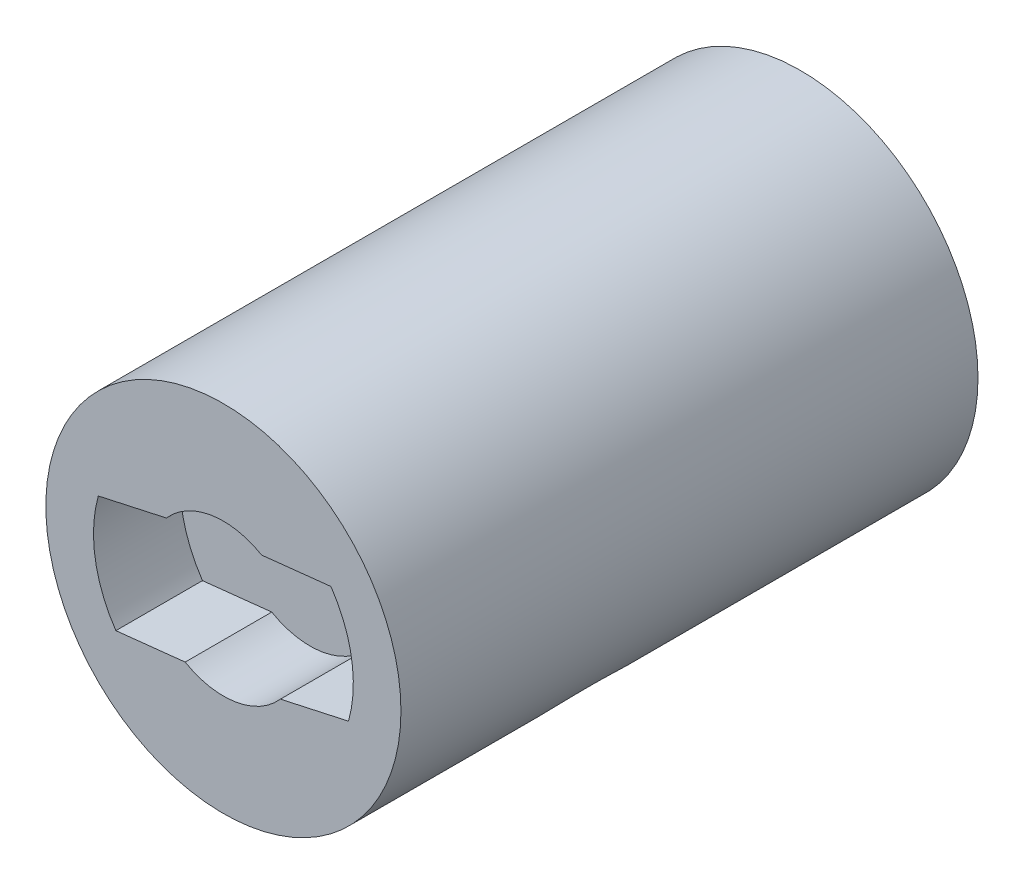
SolidWorks part; units mm, degrees
ref_plane "Спереди" through (0, 0, 0) normal (0, 0, 1) x (1, 0, 0)
ref_plane "Сверху" through (0, 0, 0) normal (0, 1, 0) x (1, 0, 0)
ref_plane "Справа" through (0, 0, 0) normal (1, 0, 0) x (0, 0, -1)
sketch "Эскиз1" plane through (0, 0, 0) normal (0, 0, 1) x (1, 0, 0)
  circle A0 centre (0, 0) radius 8.2
  dimension "D1" = 16.4
extrude "Бобышка-Вытянуть1" add sketch "Эскиз1" along normal blind 26.65
sketch "Эскиз3" plane through (0, 0, 0) normal (0, 0, -1) x (-1, 0, 0)
  circle A0 centre (0, 0) radius 5
  dimension "D1" = 10
extrude "Бобышка-Вытянуть2" add sketch "Эскиз3" along normal blind 1.5
sketch "Эскиз4" plane through (0, 0, 26.65) normal (0, 0, 1) x (1, 0, 0)
  line L8 (-2.6335, 2.3053) -> (-14.3067, -0.2584)
  line L9 (13.648, 4.299) -> (1.765, 3.0224)
  line L10 (2.6335, -2.3053) -> (14.3067, 0.2584)
  line L11 (-13.648, -4.299) -> (-1.765, -3.0224)
  line L12 (-2.6335, 2.3053) -> (-14.3067, -0.2584)
  line L13 (13.648, 4.299) -> (1.765, 3.0224)
  line L14 (2.6335, -2.3053) -> (14.3067, 0.2584)
  line L15 (-13.648, -4.299) -> (-1.765, -3.0224)
  circle A4 centre (0, 0) radius 6
  arc A8 (1.765, 3.0224) -> (-2.6335, 2.3053) centre (0, 0) ccw
  arc A9 (14.3067, 0.2584) -> (13.648, 4.299) centre (13.8669, 2.2607) ccw
  arc A10 (-1.765, -3.0224) -> (2.6335, -2.3053) centre (0, 0) ccw
  arc A11 (-14.3067, -0.2584) -> (-13.648, -4.299) centre (-13.8669, -2.2607) ccw
  arc A12 (1.765, 3.0224) -> (-2.6335, 2.3053) centre (0, 0) ccw
  arc A13 (14.3067, 0.2584) -> (13.648, 4.299) centre (13.8669, 2.2607) ccw
  arc A14 (-1.765, -3.0224) -> (2.6335, -2.3053) centre (0, 0) ccw
  arc A15 (-14.3067, -0.2584) -> (-13.648, -4.299) centre (-13.8669, -2.2607) ccw
  dimension "D2" = 12
  dimension "D1" = 0.05
extrude "Вырез-Вытянуть1" cut sketch "Эскиз4" against normal blind 4 contours L15 A14 L14 A4 L13 A12 L12
sketch "Эскиз5" plane through (0, 0, 0) normal (0, 1, 0) x (1, 0, 0)
  circle A0 centre (0, -16) radius 7 construction
  circle A1 centre (0, -16) radius 7
  circle A2 centre (0, -16) radius 6.25
  dimension "D1" = 12.5
extrude "Вырез-Вытянуть2" cut sketch "Эскиз5" against normal blind 10 from offset 1 contours A2
